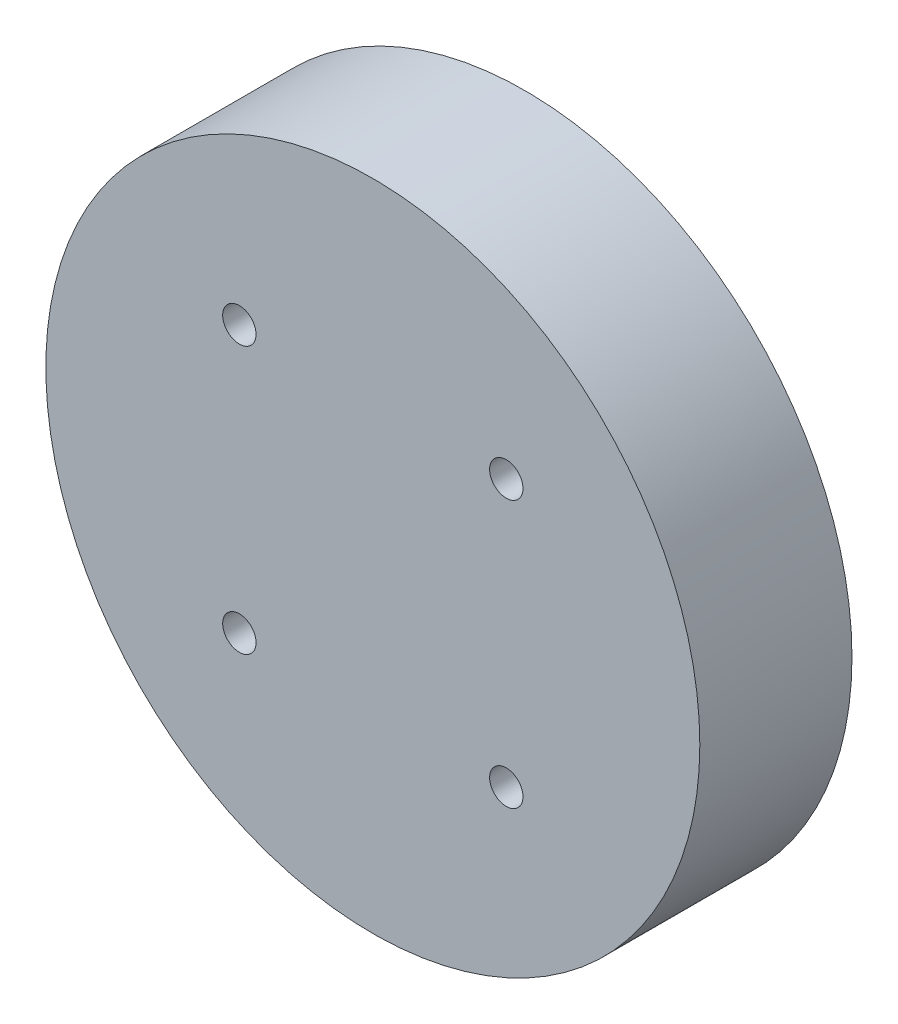
SolidWorks part; units mm, degrees
material "0.6010 (EN-GJL-100)"
ref_plane "前视基准面" through (0, 0, 0) normal (0, 0, 1) x (1, 0, 0)
ref_plane "上视基准面" through (0, 0, 0) normal (0, 1, 0) x (1, 0, 0)
ref_plane "右视基准面" through (0, 0, 0) normal (1, 0, 0) x (0, 0, -1)
sketch "草图1" plane through (0, 0, 0) normal (0, 0, 1) x (1, 0, 0)
  circle A0 centre (0, 0) radius 24.5
  dimension "D1" = 49
extrude "凸台-拉伸1" add sketch "草图1" along normal blind 11.4
sketch "草图2" plane through (0, 0, 11.4) normal (0, 0, 1) x (1, 0, 0)
  line L0 (0, 29.6541) -> (0, -32.8453) construction
  line L2 (-138.6367, 0) -> (48.3196, 0) construction
  circle A0 centre (-10, 10) radius 1.25
  circle A1 centre (10, 10) radius 1.25
  circle A2 centre (-10, -10) radius 1.25
  circle A3 centre (10, -10) radius 1.25
  point P4 (0, 0)
  point P7 (0, 0)
  point P10 (-45.1585, 0)
  point P14 (0, 0)
  point P17 (0, 0)
  dimension "D1" = 2.5
  dimension "D2" = 2.5
  dimension "D3" = 2.5
  dimension "D4" = 2.5
  dimension "D5" = 20
  dimension "D6" = 10
  dimension "D7" = 10
  dimension "D8" = 10
  dimension "D9" = 10
extrude "切除-拉伸1" cut sketch "草图2" against normal blind 8
